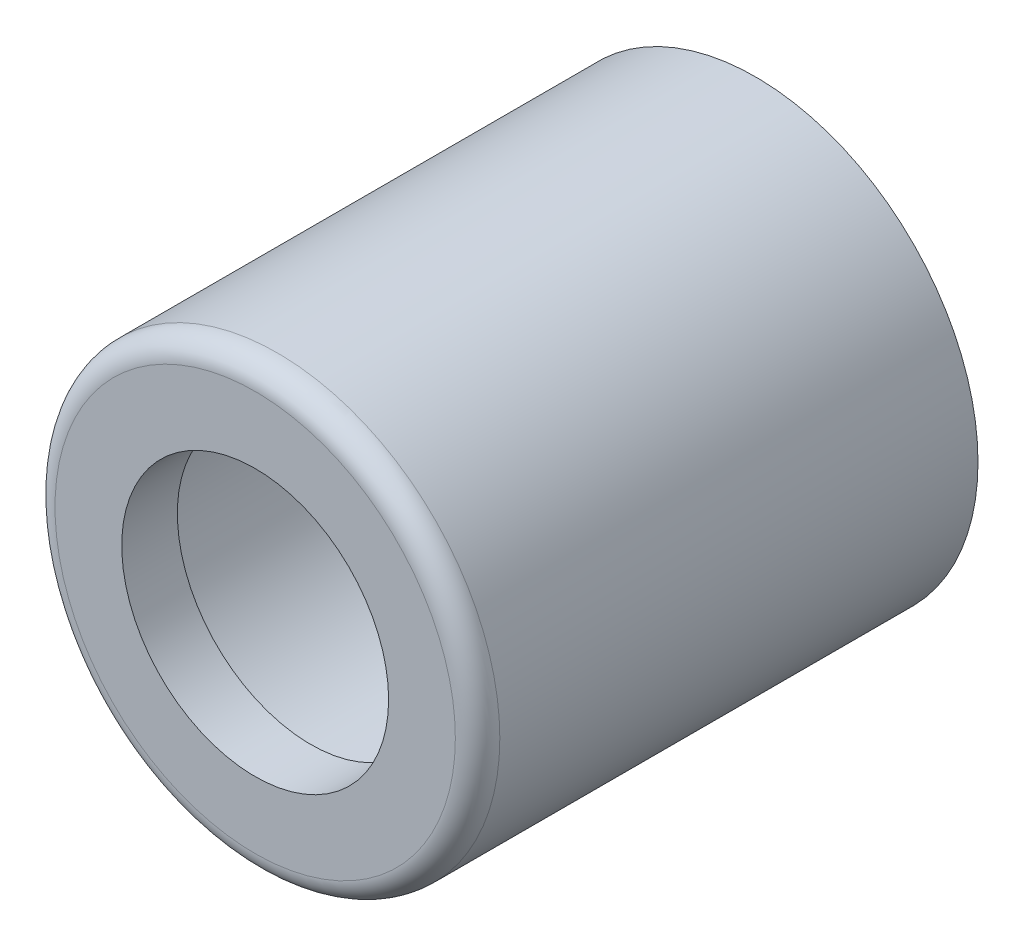
SolidWorks part; units mm, degrees
material "PVC 0.007 Plasticized"
ref_plane "Front Plane" through (0, 0, 0) normal (0, 0, 1) x (1, 0, 0)
ref_plane "Top Plane" through (0, 0, 0) normal (0, 1, 0) x (1, 0, 0)
ref_plane "Right Plane" through (0, 0, 0) normal (1, 0, 0) x (0, 0, -1)
sketch "Sketch1" plane through (0, 0, 0) normal (0, 0, 1) x (1, 0, 0)
  circle A0 centre (0, 0) radius 7.5
  circle A1 centre (0, 0) radius 10
  dimension "D1" = 15
  dimension "D2" = 20
extrude "Boss-Extrude1" add sketch "Sketch1" along normal blind 20
sketch "Sketch2" plane through (0, 0, 20) normal (0, 0, 1) x (1, 0, 0)
  circle A0 centre (0, 0) radius 10 construction
  circle A1 centre (0, 0) radius 10
extrude "Boss-Extrude2" add sketch "Sketch2" along normal blind 2.5
sketch "Sketch3" plane through (0, 0, 22.5) normal (0, 0, 1) x (1, 0, 0)
  circle A0 centre (0, 0) radius 6
  dimension "D1" = 12
extrude "Cut-Extrude1" cut sketch "Sketch3" against normal blind 2.5
fillet "Fillet1" radius 1 1 edges at (10, 0, 22.5)
